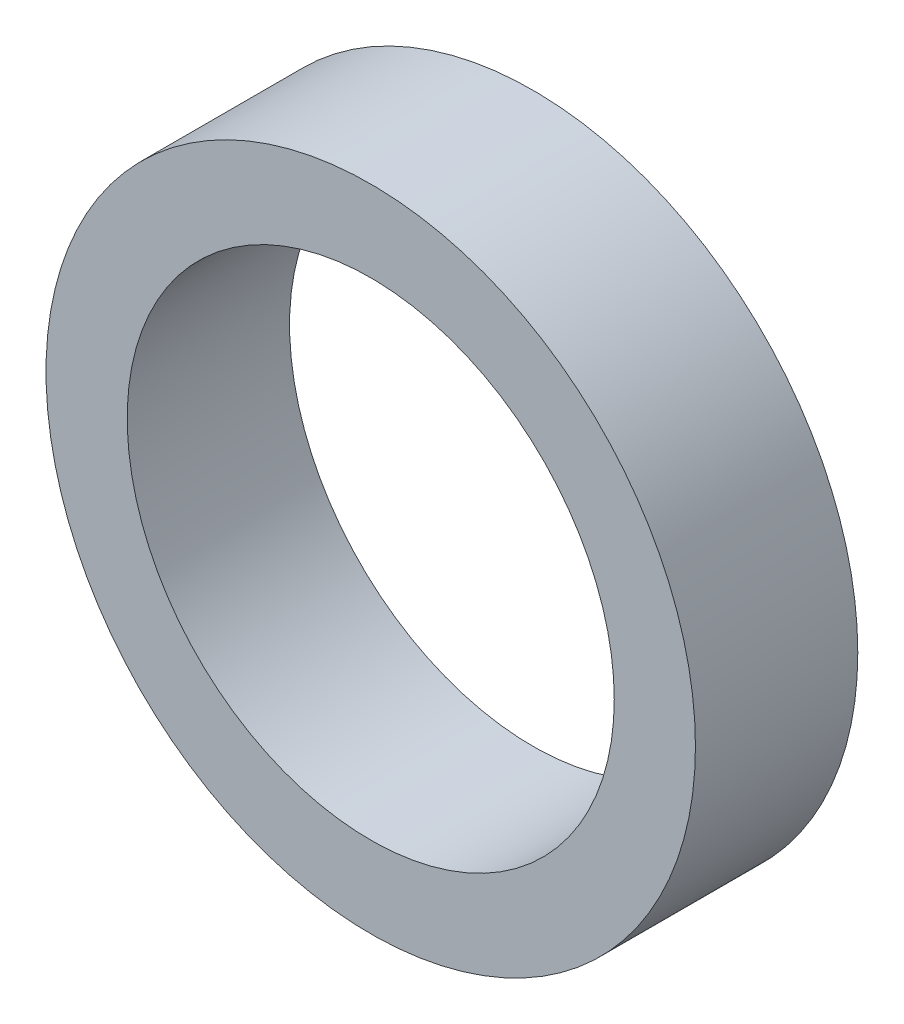
SolidWorks part; units mm, degrees
material "6061 Alloy"
ref_plane "Front Plane" through (0, 0, 0) normal (0, 0, 1) x (1, 0, 0)
ref_plane "Top Plane" through (0, 0, 0) normal (0, 1, 0) x (1, 0, 0)
ref_plane "Right Plane" through (0, 0, 0) normal (1, 0, 0) x (0, 0, -1)
sketch "Sketch1" plane through (0, 0, 0) normal (0, 0, 1) x (1, 0, 0)
  circle A0 centre (0, 0) radius 6.35
  circle A1 centre (0, 0) radius 4.7625
  dimension "D1" = 12.7
  dimension "D2" = 9.525
extrude "Boss-Extrude1" add sketch "Sketch1" along normal blind 3.175
